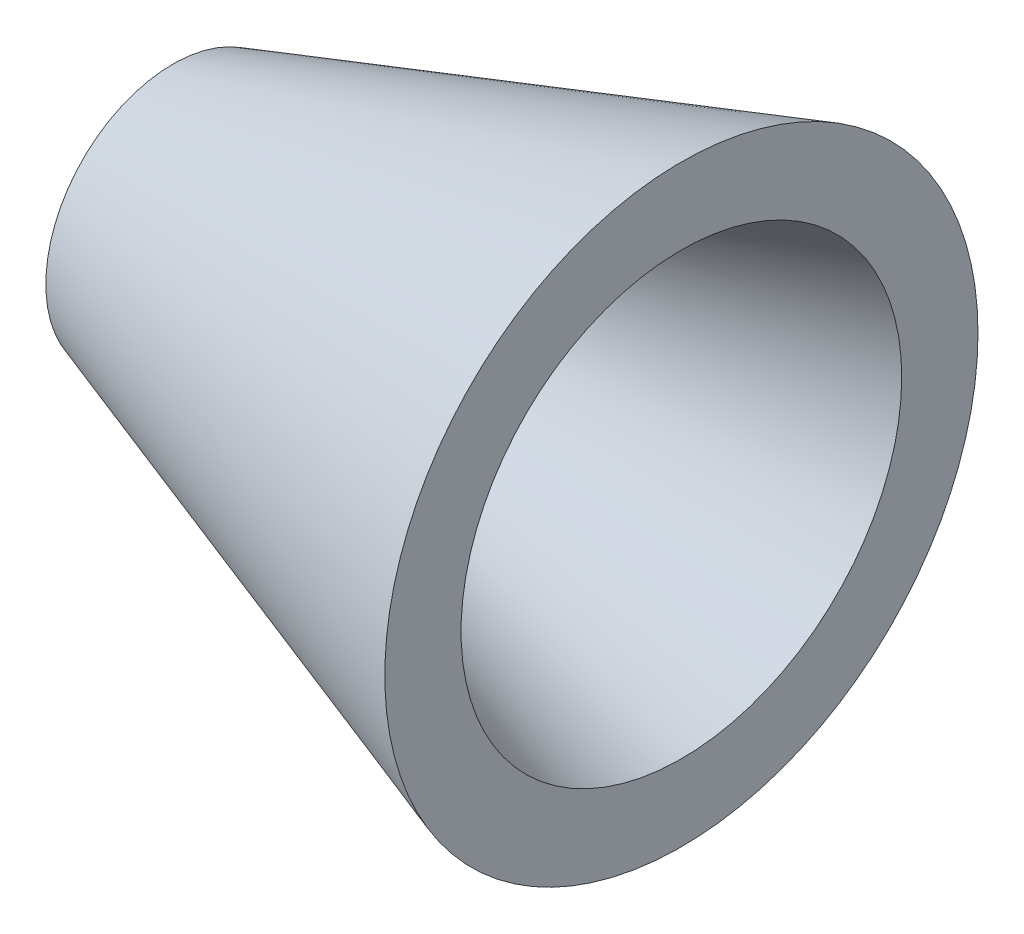
SolidWorks part; units mm, degrees
material "1060 Alloy"
ref_plane "Front Plane" through (0, 0, 0) normal (0, 0, 1) x (1, 0, 0)
ref_plane "Top Plane" through (0, 0, 0) normal (0, 1, 0) x (1, 0, 0)
ref_plane "Right Plane" through (0, 0, 0) normal (1, 0, 0) x (0, 0, -1)
sketch "Sketch1" plane through (0, 0, 0) normal (0, 0, 1) x (1, 0, 0)
  line L4 (-140, 0) -> (-200, 0)
  line L5 (-200, 100) -> (200, 233.3333)
  line L6 (200, 233.3333) -> (200, 173.3333)
  line L7 (200, 173.3333) -> (-140, 60)
  line L8 (-140, 60) -> (-140, 0)
  line L9 (-200, 0) -> (-200, 100)
  point P4 (0, 0)
  point P7 (0, 166.6667)
  point P9 (0, 0)
  dimension "D1" = 60
  dimension "D2" = 60
  dimension "D3" = 100
  dimension "D4" = 400
  dimension "D5" = 60
revolve "Revolve1" add sketch "Sketch1" angle 360 about L4
sketch "Sketch3" plane through (-200, 0, 0) normal (-1, 0, 0) x (0, 0, 1)
  point P1 (0, 0)
  point P4 (0, 0)
